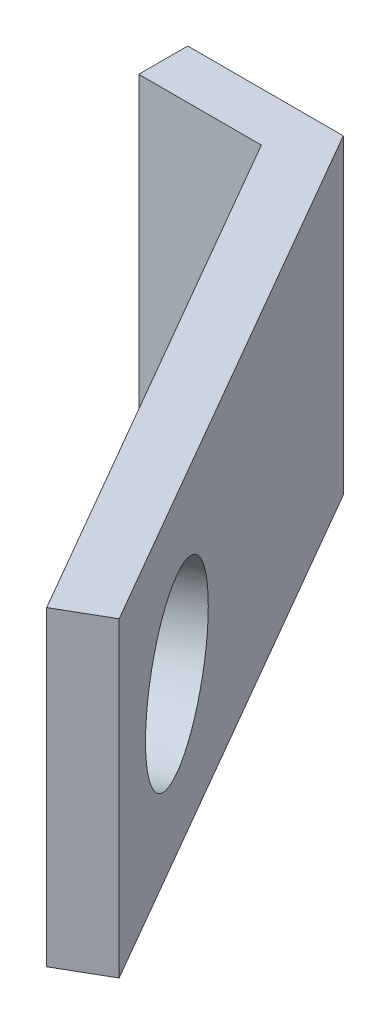
SolidWorks part; units mm, degrees
ref_plane "Front Plane" through (0, 0, 0) normal (0, 0, 1) x (1, 0, 0)
ref_plane "Top Plane" through (0, 0, 0) normal (0, 1, 0) x (1, 0, 0)
ref_plane "Right Plane" through (0, 0, 0) normal (1, 0, 0) x (0, 0, -1)
sketch "Sketch1" plane through (0, 0, 0) normal (0, 0, 1) x (1, 0, 0)
  line L1 (0, 0) -> (6.35, 0)
  line L2 (0, 0) -> (0, 12.7)
  line L3 (0, 12.7) -> (6.35, 12.7)
  line L4 (6.35, 0) -> (6.35, 12.7)
  dimension "D1" = 12.7
  dimension "D2" = 6.35
extrude "Boss-Extrude1" add sketch "Sketch1" along normal blind 2
sketch "Sketch2" plane through (0, 0, 0) normal (0, -1, 0) x (1, 0, 0)
  line L0 (6.35, 0) -> (18.85, 21.6506)
  line L1 (18.85, 21.6506) -> (16.975, 22.7332)
  line L2 (16.975, 22.7332) -> (3.85, 0)
  line L3 (0, 0) -> (6.35, 0) construction
  line L4 (3.85, 0) -> (6.35, 0)
  line L5 (0, 2) -> (6.35, 2) construction
  dimension "D1" = 2.5
  dimension "D2" = 25
  dimension "D3" = 120
extrude "Boss-Extrude2" add sketch "Sketch2" against normal up to surface (12.7 mm away) up to face at (3.175, 12.7, 1)
sketch "Sketch3" plane through (2.8875, 0, -1.6671) normal (-0.866, 0, 0.5) x (0.5, 0, 0.866)
  line L1 (4.2344, 0) -> (4.2344, 12.7) construction
  line L4 (28.175, 12.7) -> (28.175, 0) construction
  circle A1 centre (21.7344, 6.35) radius 3.5
  point P4 (0, 0)
  point P5 (28.175, 6.35)
  point P6 (0, 0)
  dimension "D1" = 7
  dimension "D2" = 17.5
extrude "Cut-Extrude1" cut sketch "Sketch3" against normal through all
